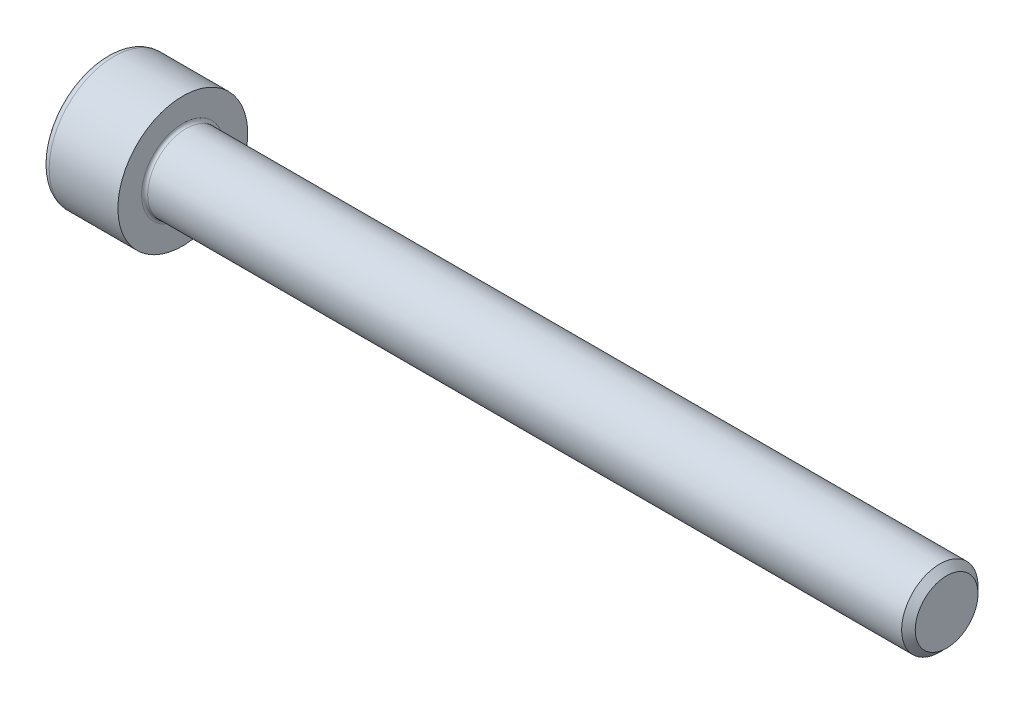
SolidWorks part; units mm, degrees
ref_plane "Plane1" through (0, 0, 0) normal (0, 0, 1) x (1, 0, 0)
ref_plane "Plane2" through (0, 0, 0) normal (0, 1, 0) x (1, 0, 0)
ref_plane "Plane3" through (0, 0, 0) normal (1, 0, 0) x (0, 0, -1)
sketch "BodySke" plane through (0, 0, 0) normal (0, 0, 1) x (1, 0, 0)
  line L0 (0, 0) -> (0, 4.25)
  line L1 (0, 4.25) -> (5, 4.25)
  line L2 (5, 4.25) -> (5, 2.5)
  line L3 (5, 2.5) -> (54.555, 2.5)
  line L4 (55, 2.055) -> (55, 0)
  line L5 (55, 0) -> (0, 0)
  line L6 (-31.75, 0) -> (127, 0) construction
  line L8 (55, 2.055) -> (54.555, 2.5)
  line L10 (55, -2.055) -> (54.555, -2.5) construction
  line L11 (5.8, 9.525) -> (5.8, 3.175) construction
  line L12 (33, 9.525) -> (33, 3.175) construction
  line L13 (-5, 9.525) -> (-5, 3.175) construction
  dimension "Diameter" = 5
  dimension "Head_ht" = 5
  dimension "Length" = 50
  dimension "Body_ch_ang" = 45
  dimension "Head_dia" = 8.5
  dimension "Minor_dia" = 4.11
  dimension "Advance" = 0.8
  dimension "Thread_nom" = 22
  dimension "Thread_length" = 60
revolve "Base-Revolve" add sketch "BodySke"
cosmetic thread "ThreadCosmetic" [suppressed]
fillet "Fillet1" radius 0.2 1 edges at (5, 0, 2.5)
fillet "Fillet2" radius 0.5 1 edges at (0, 0, 4.25)
sketch "Sketch2" plane through (0, 0, 0) normal (0, 0, 1) x (1, 0, 0)
  line L0 (0, 2.01) -> (2.5, 2.01)
  line L1 (2.5, 2.01) -> (3.6605, 0)
  line L2 (-31.75, 0) -> (127, 0) construction
  line L3 (3.6605, 0) -> (0, 0)
  line L4 (0, 0) -> (0, 2.01)
  line L6 (0, 0) -> (47.625, 0) construction
  dimension "D1" = 2.01
  dimension "D2" = 60
  dimension "Depth" = 2.5
revolve "Hex-PreBroach" cut sketch "Sketch2" angle 360 about L6
sketch "Sketch3" plane through (0, 0, 0) normal (-1, 0, 0) x (0, 0.5, 0.866)
  line L0 (1.1605, 2.01) -> (-1.1605, 2.01)
  line L1 (-1.1605, 2.01) -> (-2.3209, 0)
  line L2 (1.1605, 2.01) -> (2.3209, 0)
  line L3 (1.1605, -2.01) -> (2.3209, 0)
  line L4 (1.1605, -2.01) -> (-1.1605, -2.01)
  line L5 (-1.1605, -2.01) -> (-2.3209, 0)
  dimension "D1" = 2.01
  dimension "D2" = 2.01
  dimension "Hex_size" = 4.02
extrude "Hex" cut sketch "Sketch3" against normal blind 2.5
sketch "ThdSchSke" plane through (0, 0, 0) normal (0, 0, 1) x (1, 0, 0)
  line L0 (33, -2.055) -> (32.6884, -2.5)
  line L1 (33, -2.055) -> (33.3116, -2.5)
  line L2 (33.3116, -2.5) -> (33.3116, -3.125)
  line L3 (-3.175, 0) -> (5.1513, 0) construction
  line L4 (0, 3.75) -> (0, -3.75) construction
  line L5 (33.3116, -3.125) -> (32.6884, -3.125)
  line L6 (32.6884, -3.125) -> (32.6884, -2.5)
  dimension "Thread_minor" = 4.11
  dimension "Diameter" = 5
  dimension "Start" = 33
  dimension "SideAngle" = 55
  dimension "VeeAngle" = 70
  dimension "Overcut" = 6.25
revolve "ThreadSchematic" [suppressed] cut sketch "ThdSchSke" angle 360 about L3
pattern_linear "ThdSchPat" [suppressed]
equation "\"D2@Sketch3\" = \"Hex_size@Sketch3\" / 2"
equation "\"D1@Sketch3\" = \"Hex_size@Sketch3\" / 2"
equation "\"D1@Sketch2\" = \"Hex_size@Sketch3\" / 2"
equation "\"Thread_minor@ThreadCosmetic\"  =  \"Minor_dia@BodySke\""
equation "\"Depth@Sketch2\" =  \"Key_eng@Hex\""
equation "\"Thread_length@ThreadCosmetic\" = ((sgn( (\"Length@BodySke\" - \"Advance@BodySke\" * 3.0) - \"Thread_nom@BodySke\" )-1)*( (\"Length@BodySke\" - \"Advance@BodySke\" * 3.0) - \"Thread_nom@BodySke\" ))/-2+ \"Thread_nom@BodySke\""
equation "\"Thread_minor@ThdSchSke\" = \"Minor_dia@BodySke\""
equation "\"Diameter@ThdSchSke\" = \"Diameter@BodySke\""
equation "\"Overcut@ThdSchSke\" = \"Diameter@BodySke\" * 1.25"
equation "\"Start@ThdSchSke\" = \"Head_ht@BodySke\" + \"Length@BodySke\" - \"Thread_length@ThreadCosmetic\"  '---Non-countersunk---"
equation "\"Num_threads@ThdSchPat\" = int( \"Thread_length@ThreadCosmetic\" / \"Advance@BodySke\" + 0.999 )  + 1"
equation "\"Advance@ThdSchPat\" = \"Thread_length@ThreadCosmetic\" /  (\"Num_threads@ThdSchPat\" - 1) 'relax it"
equation "\"Num_threads@ThdSchPat\" = \"Num_threads@ThdSchPat\" - sgn( \"Num_threads@ThdSchPat\" - 1) '---chamfered tips only---"
